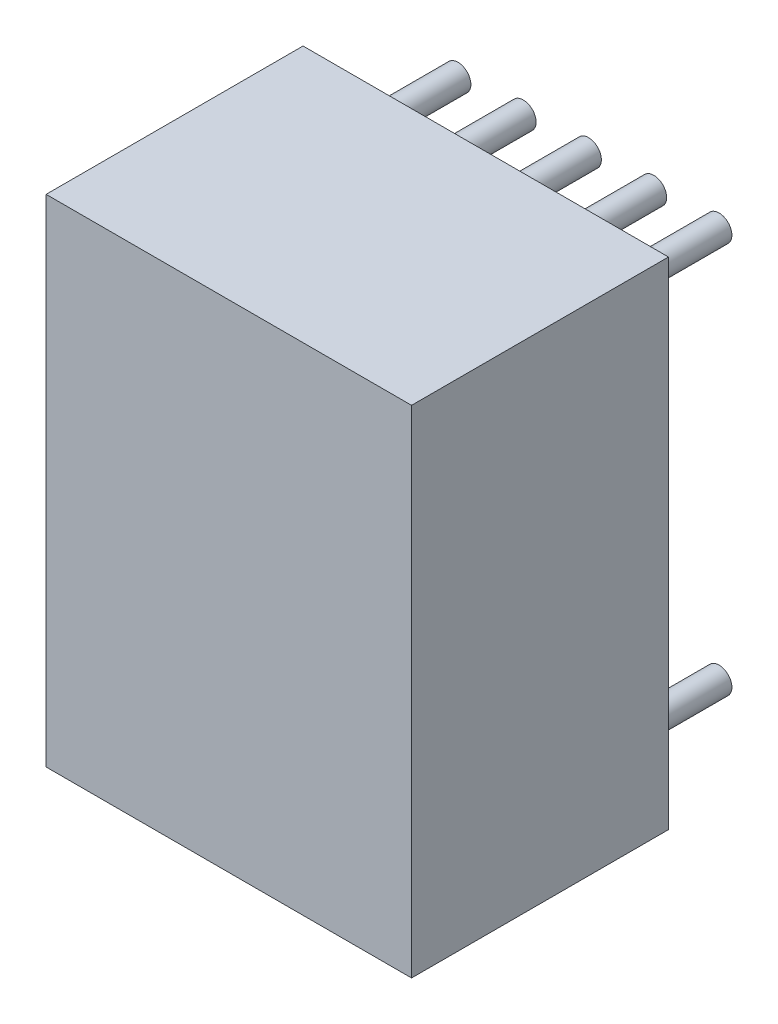
SolidWorks part; units mm, degrees
ref_plane "Front Plane" through (0, 0, 0) normal (0, 0, 1) x (1, 0, 0)
ref_plane "Top Plane" through (0, 0, 0) normal (0, 1, 0) x (1, 0, 0)
ref_plane "Right Plane" through (0, 0, 0) normal (1, 0, 0) x (0, 0, -1)
sketch "Sketch1" plane through (0, 0, 0) normal (0, 0, 1) x (1, 0, 0)
  line L0 (-1.016, 8.636) -> (-1.016, -1.016)
  line L1 (-1.016, -1.016) -> (6.096, -1.016)
  line L2 (6.096, -1.016) -> (6.096, 8.636)
  line L3 (6.096, 8.636) -> (-1.016, 8.636)
extrude "Component_Outline" add sketch "Sketch1" along normal blind 5 separate body
sketch "Sketch2" plane through (0, 0, 0) normal (0, 0, 1) x (1, 0, 0)
  circle A0 centre (0, 0) radius 0.25
extrude "1" add sketch "Sketch2" against normal blind 2 separate body
sketch "Sketch3" plane through (0, 0, 0) normal (0, 0, 1) x (1, 0, 0)
  circle A0 centre (1.27, 0) radius 0.25
extrude "2" add sketch "Sketch3" against normal blind 2 separate body
sketch "Sketch4" plane through (0, 0, 0) normal (0, 0, 1) x (1, 0, 0)
  circle A0 centre (2.54, 0) radius 0.25
extrude "3" add sketch "Sketch4" against normal blind 2 separate body
sketch "Sketch5" plane through (0, 0, 0) normal (0, 0, 1) x (1, 0, 0)
  circle A0 centre (3.81, 0) radius 0.25
extrude "4" add sketch "Sketch5" against normal blind 2 separate body
sketch "Sketch6" plane through (0, 0, 0) normal (0, 0, 1) x (1, 0, 0)
  circle A0 centre (5.08, 0) radius 0.25
extrude "5" add sketch "Sketch6" against normal blind 2 separate body
sketch "Sketch7" plane through (0, 0, 0) normal (0, 0, 1) x (1, 0, 0)
  circle A0 centre (5.08, 7.62) radius 0.25
extrude "6" add sketch "Sketch7" against normal blind 2 separate body
sketch "Sketch8" plane through (0, 0, 0) normal (0, 0, 1) x (1, 0, 0)
  circle A0 centre (3.81, 7.62) radius 0.25
extrude "7" add sketch "Sketch8" against normal blind 2 separate body
sketch "Sketch9" plane through (0, 0, 0) normal (0, 0, 1) x (1, 0, 0)
  circle A0 centre (2.54, 7.62) radius 0.25
extrude "8" add sketch "Sketch9" against normal blind 2 separate body
sketch "Sketch10" plane through (0, 0, 0) normal (0, 0, 1) x (1, 0, 0)
  circle A0 centre (1.27, 7.62) radius 0.25
extrude "9" add sketch "Sketch10" against normal blind 2 separate body
sketch "Sketch11" plane through (0, 0, 0) normal (0, 0, 1) x (1, 0, 0)
  circle A0 centre (0, 7.62) radius 0.25
extrude "10" add sketch "Sketch11" against normal blind 2 separate body
sketch3d "3DSketch1"
  line L0 (0, 0, 0) -> (1, 0, 0)
  line L1 (0, 0, 0) -> (0, 1, 0)
  line L2 (0, 0, 0) -> (0, 0, 1)
  point P0 (0, 0, 0)
